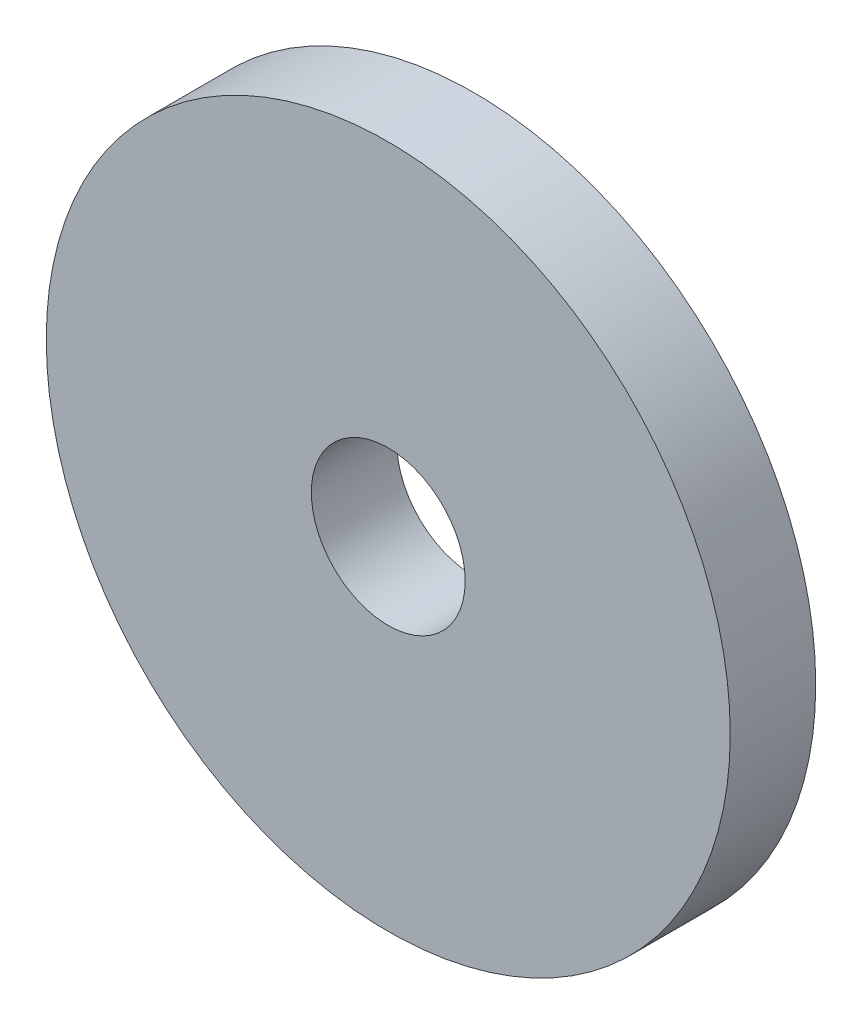
SolidWorks part; units mm, degrees
ref_plane "Front Plane" through (0, 0, 0) normal (0, 0, 1) x (1, 0, 0)
ref_plane "Top Plane" through (0, 0, 0) normal (0, 1, 0) x (1, 0, 0)
ref_plane "Right Plane" through (0, 0, 0) normal (1, 0, 0) x (0, 0, -1)
sketch "Sketch2" plane through (0, 0, 0) normal (0, 0, 1) x (1, 0, 0)
  circle A0 centre (0, 0) radius 20
  circle A1 centre (0, 0) radius 4.5
  dimension "D1" = 9
  dimension "D2" = 40
extrude "Boss-Extrude1" add sketch "Sketch2" along normal mid plane 5
